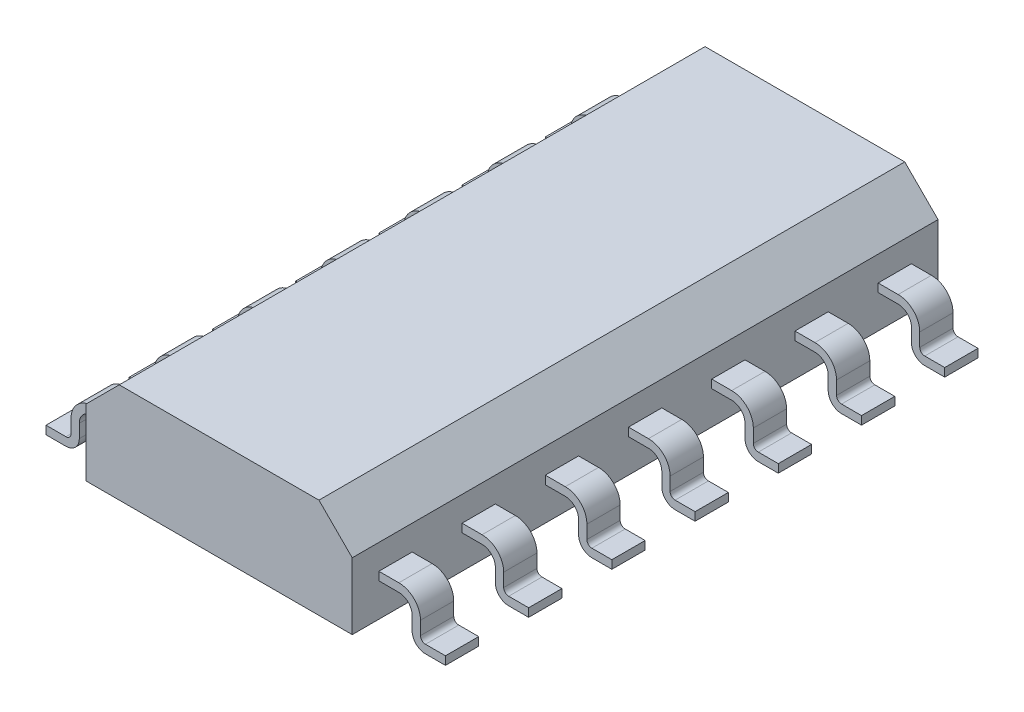
SolidWorks part; units mm, degrees
ref_plane "Front Plane" through (0, 0, 0) normal (0, 0, 1) x (1, 0, 0)
ref_plane "Top Plane" through (0, 0, 0) normal (0, 1, 0) x (1, 0, 0)
ref_plane "Right Plane" through (0, 0, 0) normal (1, 0, 0) x (0, 0, -1)
sketch "Sketch1" plane through (0, 0, 0) normal (0, 0, 1) x (1, 0, 0)
  line L0 (-2, -0.75) -> (2, -0.75)
  line L1 (2, -0.75) -> (2, 0.25)
  line L2 (2, 0.25) -> (1.5, 0.75)
  line L3 (1.5, 0.75) -> (-1.5, 0.75)
  line L4 (-1.5, 0.75) -> (-2, 0.25)
  line L5 (-2, 0.25) -> (-2, -0.75)
  line L6 (0, -0.75) -> (0, 0.75) construction
  dimension "D1" = 4
  dimension "D2" = 3
  dimension "D3" = 1
  dimension "D4" = 1
  dimension "D5" = 0.7071
extrude "Extrude1" add sketch "Sketch1" along normal mid plane 8.8
ref_plane "Plane4" through (0, 0, 4) normal (0, 0, 1) x (1, 0, 0)
sketch "Sketch2" plane through (0, 0, 4) normal (0, 0, 1) x (1, 0, 0)
  line L0 (-2.5, -0.65) -> (-2.5, -0.45)
  line L1 (-2.3, -0.25) -> (-2, -0.25)
  line L2 (-2, -0.25) -> (-2, -0.125)
  line L3 (-2, -0.125) -> (-2.3, -0.125)
  line L4 (-2.625, -0.45) -> (-2.625, -0.65)
  line L5 (-2.7, -0.725) -> (-3, -0.725)
  line L6 (-3, -0.725) -> (-3, -0.85)
  line L7 (-3, -0.85) -> (-2.7, -0.85)
  arc A0 (-2.3, -0.25) -> (-2.5, -0.45) centre (-2.3, -0.45) ccw
  arc A1 (-2.3, -0.125) -> (-2.625, -0.45) centre (-2.3, -0.45) ccw
  arc A2 (-2.7, -0.725) -> (-2.625, -0.65) centre (-2.7, -0.65) ccw
  arc A3 (-2.7, -0.85) -> (-2.5, -0.65) centre (-2.7, -0.65) ccw
  point P2 (0, 0)
  dimension "D5" = 0.2
  dimension "D6" = 0.325
  dimension "D7" = 0.2
  dimension "D8" = 0.075
  dimension "D1" = 0.3
  dimension "D2" = 0.3
  dimension "D3" = 0.125
  dimension "D4" = 0.2
  dimension "D9" = 0.2
  dimension "D10" = 0.325
  dimension "D11" = 0.2
  dimension "D12" = 0.125
  dimension "D13" = 2
  dimension "D14" = 0.2
  dimension "D15" = 0.2
extrude "Extrude2" add sketch "Sketch2" against normal blind 0.5
pattern_linear "LPattern1" count 7 spacing 1.25 along (0, 0, -1) of "Extrude2"
mirror "Mirror1" about plane through (0, 0, 0) normal (1, 0, 0) of "LPattern1", "Extrude2"
